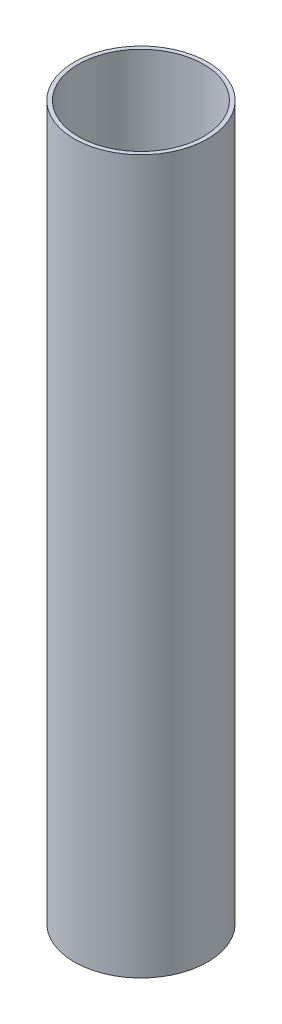
SolidWorks part; units mm, degrees
material "6063-T6"
ref_plane "Front Plane" through (0, 0, 0) normal (0, 0, 1) x (1, 0, 0)
ref_plane "Top Plane" through (0, 0, 0) normal (0, 1, 0) x (1, 0, 0)
ref_plane "Right Plane" through (0, 0, 0) normal (1, 0, 0) x (0, 0, -1)
sketch "Sketch1" plane through (0, 0, 0) normal (0, 1, 0) x (1, 0, 0)
  circle A0 centre (0, 0) radius 50
  circle A1 centre (0, 0) radius 47
  dimension "D1" = 100
  dimension "D2" = 3
extrude "Boss-Extrude1" add sketch "Sketch1" along normal blind 535
